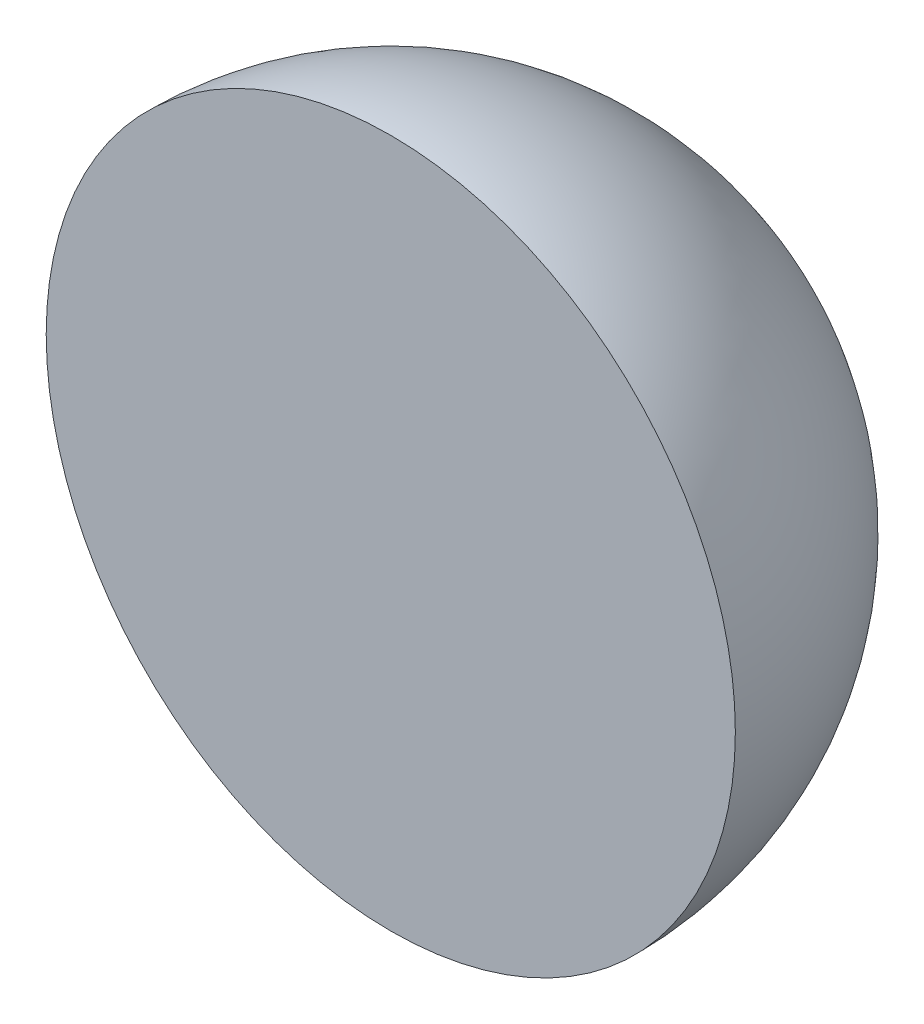
SolidWorks part; units mm, degrees
ref_plane "前基準面" through (0, 0, 0) normal (0, 0, 1) x (1, 0, 0)
ref_plane "上基準面" through (0, 0, 0) normal (0, 1, 0) x (1, 0, 0)
ref_plane "右基準面" through (0, 0, 0) normal (1, 0, 0) x (0, 0, -1)
sketch "草圖1" plane through (0, 0, 0) normal (0, 1, 0) x (1, 0, 0)
  line L0 (0, 0) -> (0, 20)
  line L1 (0, 0) -> (-20, 0)
  arc A0 (0, 20) -> (-20, 0) centre (0, 0) ccw
  dimension "D1" = 40
revolve "旋轉1" add sketch "草圖1" angle 360 about L0
